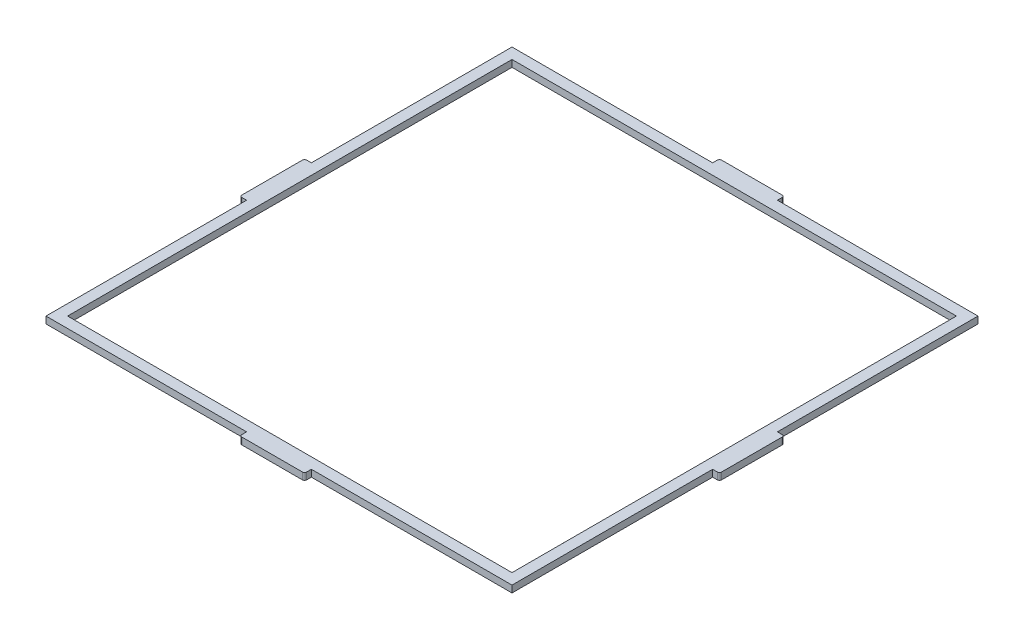
SolidWorks part; units mm, degrees
ref_plane "Front Plane" through (0, 0, 0) normal (0, 0, 1) x (1, 0, 0)
ref_plane "Top Plane" through (0, 0, 0) normal (0, 1, 0) x (1, 0, 0)
ref_plane "Right Plane" through (0, 0, 0) normal (1, 0, 0) x (0, 0, -1)
sketch "Sketch1" plane through (0, 0, 0) normal (0, 1, 0) x (1, 0, 0)
  line L1 (-107.955, -107.955) -> (107.955, -107.955)
  line L2 (-107.955, -107.955) -> (-107.955, 107.955)
  line L3 (-107.955, 107.955) -> (107.955, 107.955)
  line L4 (107.955, -107.955) -> (107.955, 107.955)
  line L5 (-107.955, -107.955) -> (107.955, 107.955) construction
  line L6 (-107.955, 107.955) -> (107.955, -107.955) construction
  point P0 (0, 0)
  dimension "D1" = 215.91
  dimension "D2" = 215.91
extrude "Boss-Extrude1" add sketch "Sketch1" along normal blind 3.175
sketch "Sketch2" plane through (0, 3.175, 0) normal (0, 1, 0) x (1, 0, 0)
  line L0 (107.955, 107.955) -> (-107.955, 107.955) construction
  line L1 (-102.955, -102.955) -> (102.955, -102.955)
  line L2 (-102.955, -102.955) -> (-102.955, 102.955)
  line L3 (-102.955, 102.955) -> (102.955, 102.955)
  line L4 (102.955, -102.955) -> (102.955, 102.955)
  line L5 (-102.955, -102.955) -> (102.955, 102.955) construction
  line L6 (-102.955, 102.955) -> (102.955, -102.955) construction
  line L7 (-107.955, 107.955) -> (-107.955, -107.955) construction
  point P0 (0, 0)
  dimension "D1" = 5
  dimension "D2" = 5
extrude "Cut-Extrude1" cut sketch "Sketch2" against normal through all
ref_plane "Plane1" through (-107.955, 0, -107.955) normal (0, 0, 1) x (1, 0, 0)
sketch "Sketch4" plane through (0, 3.175, 0) normal (0, 1, 0) x (1, 0, 0)
  line L0 (0, 0) -> (-107.955, 0) construction
  line L1 (-107.955, 107.955) -> (-107.955, -107.955) construction
  line L2 (-107.955, 0) -> (0, 0) construction
  line L3 (0, 0) -> (0, -107.955) construction
  line L4 (-107.955, -107.955) -> (107.955, -107.955) construction
  line L5 (-107.955, -15) -> (-111.13, -15)
  line L6 (-107.955, 0) -> (-111.13, 0) construction
  line L7 (-107.955, -15) -> (-107.955, 15)
  line L8 (-107.955, 15) -> (-111.13, 15)
  line L9 (-111.13, -15) -> (-111.13, 15)
  line L10 (-15, 111.13) -> (15, 111.13)
  line L11 (-15, -107.955) -> (15, -107.955)
  line L12 (-15, -107.955) -> (-15, -111.13)
  line L13 (-15, -111.13) -> (15, -111.13)
  line L14 (15, -107.955) -> (15, -111.13)
  line L15 (15, 107.955) -> (15, 111.13)
  line L16 (-15, 107.955) -> (15, 107.955)
  line L17 (-15, 107.955) -> (-15, 111.13)
  line L18 (107.955, -15) -> (107.955, 15)
  line L19 (107.955, 15) -> (111.13, 15)
  line L20 (111.13, -15) -> (111.13, 15)
  line L21 (107.955, -15) -> (111.13, -15)
  point P11 (-109.5425, 0)
  point P19 (0, -107.955)
  point P20 (15, -109.5425)
  dimension "D1" = 15
  dimension "D2" = 3.175
  dimension "D3" = 30
  dimension "D4" = 3.175
extrude "Boss-Extrude2" add sketch "Sketch4" against normal blind 3.175
fillet "Fillet1" radius 1 8 edges at (-111.13, 1.5875, 15) (-111.13, 1.5875, -15) (15, 1.5875, 111.13) (-15, 1.5875, 111.13) (111.13, 1.5875, 15) (111.13, 1.5875, -15) (15, 1.5875, -111.13) (-15, 1.5875, -111.13)
